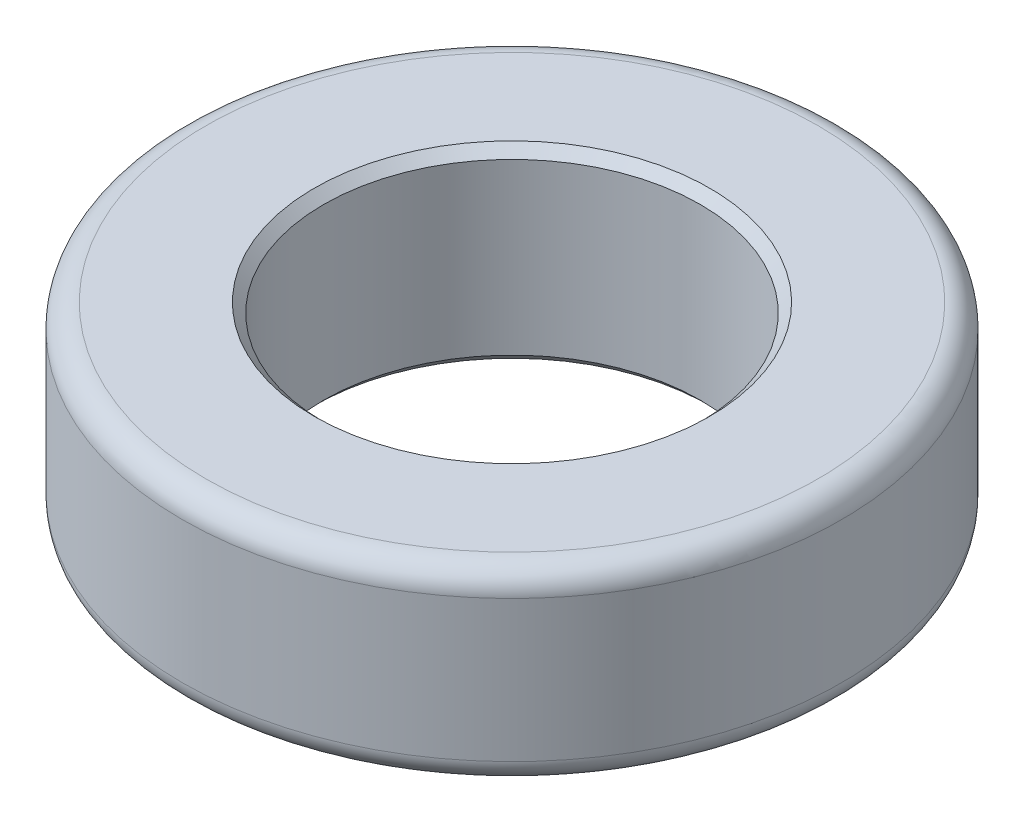
SolidWorks part; units mm, degrees
material "1023 Carbon Steel Sheet (SS)"
ref_plane "Front Plane" through (0, 0, 0) normal (0, 0, 1) x (1, 0, 0)
ref_plane "Top Plane" through (0, 0, 0) normal (0, 1, 0) x (1, 0, 0)
ref_plane "Right Plane" through (0, 0, 0) normal (1, 0, 0) x (0, 0, -1)
sketch "Sketch1" plane through (0, 0, 0) normal (0, 1, 0) x (1, 0, 0)
  circle A0 centre (0, 0) radius 7
  circle A1 centre (0, 0) radius 4
  dimension "D1" = 8
  dimension "D2" = 14
extrude "Boss-Extrude1" add sketch "Sketch1" along normal blind 4
chamfer "Chamfer1" distance 0.2 angle 45 2 edges at (0, 0, 4) (0, 4, 4)
fillet "Fillet1" radius 0.5 2 edges at (0, 0, 7) (0, 4, 7)
